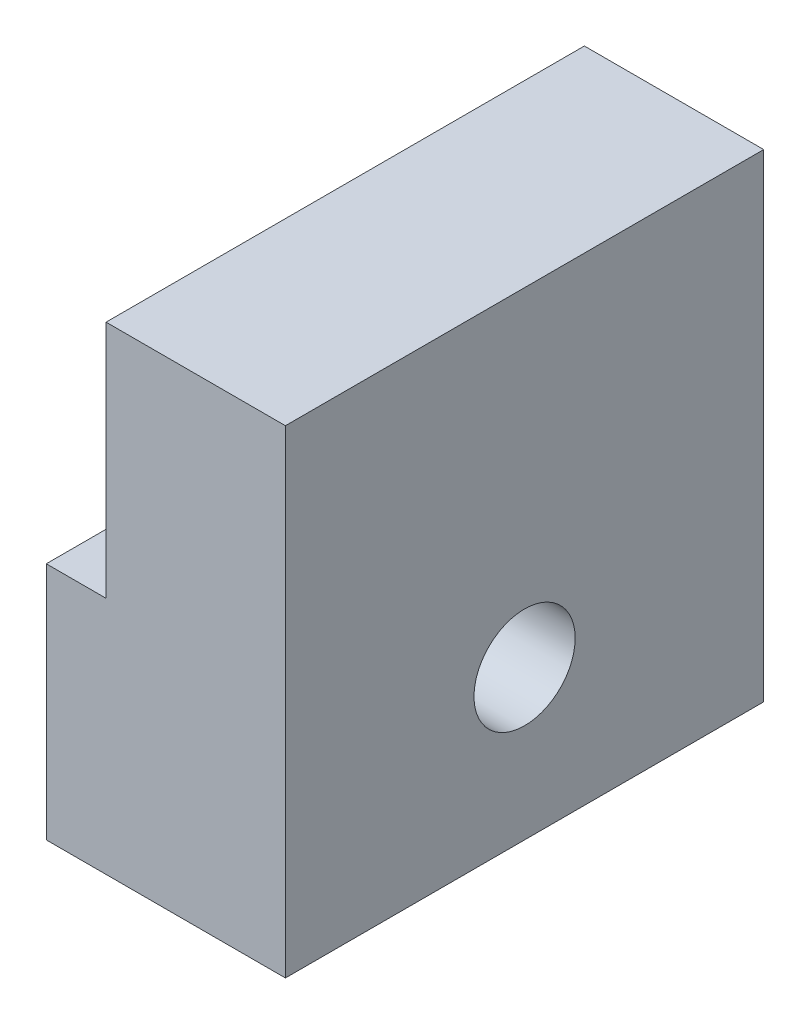
SolidWorks part; units mm, degrees
material "Plain Carbon Steel"
ref_plane "Front Plane" through (0, 0, 0) normal (0, 0, 1) x (1, 0, 0)
ref_plane "Top Plane" through (0, 0, 0) normal (0, 1, 0) x (1, 0, 0)
ref_plane "Right Plane" through (0, 0, 0) normal (1, 0, 0) x (0, 0, -1)
sketch "Sketch1" plane through (0, 0, 0) normal (1, 0, 0) x (0, 0, -1)
  line L1 (-25.4, -25.4) -> (25.4, -25.4)
  line L2 (-25.4, -25.4) -> (-25.4, 25.4)
  line L3 (-25.4, 25.4) -> (25.4, 25.4)
  line L4 (25.4, -25.4) -> (25.4, 25.4)
  line L5 (-25.4, -25.4) -> (25.4, 25.4) construction
  line L6 (-25.4, 25.4) -> (25.4, -25.4) construction
  circle A0 centre (0, -9.525) radius 5.3721
  point P0 (0, 0)
  dimension "D2" = 10.7442
  dimension "D1" = 50.8
  dimension "D3" = 15.875
extrude "Boss-Extrude1" add sketch "Sketch1" along normal blind 25.4
sketch "Sketch2" plane through (0, 0, 0) normal (-1, 0, 0) x (0, 0, 1)
  line L0 (25.4, 25.4) -> (25.4, -25.4) construction
  line L1 (-25.4, 25.4) -> (25.4, 25.4)
  line L2 (-25.4, 25.4) -> (-25.4, 0)
  line L3 (-25.4, 0) -> (25.4, 0)
  line L4 (25.4, 25.4) -> (25.4, 0)
extrude "Cut-Extrude1" cut sketch "Sketch2" against normal blind 6.35
sketch "Sketch3" plane through (6.35, 0, 0) normal (-1, 0, 0) x (0, 0, 1)
  line L0 (-25.4, 12.7) -> (25.4, 12.7)
  line L1 (-25.4, 25.4) -> (-25.4, 0) construction
  line L2 (25.4, 0) -> (25.4, 25.4) construction
  circle A0 centre (0, 12.7) radius 4.7625
  dimension "D1" = 9.525
extrude "Cut-Extrude2" cut sketch "Sketch3" against normal blind 12.7 contours A0
